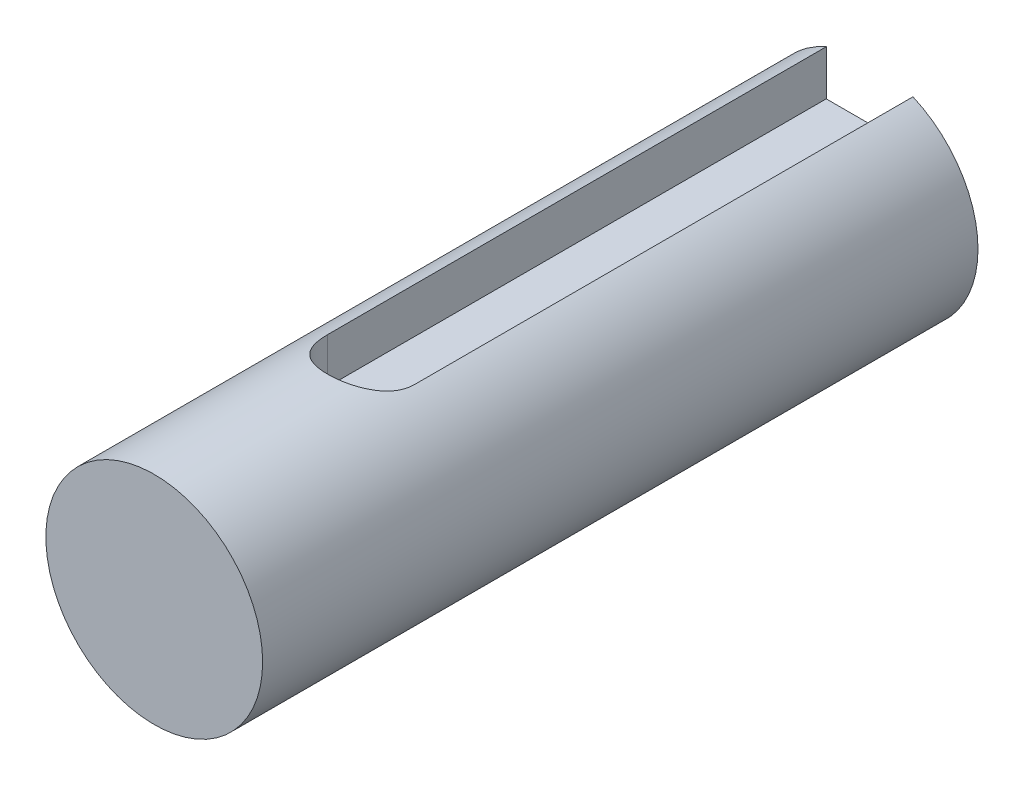
SolidWorks part; units mm, degrees
material "1023 Carbon Steel Sheet (SS)"
ref_plane "Front Plane" through (0, 0, 0) normal (0, 0, 1) x (1, 0, 0)
ref_plane "Top Plane" through (0, 0, 0) normal (0, 1, 0) x (1, 0, 0)
ref_plane "Right Plane" through (0, 0, 0) normal (1, 0, 0) x (0, 0, -1)
sketch "Sketch2" plane through (0, 0, 0) normal (0, 0, 1) x (1, 0, 0)
  line L1 (0, 0) -> (60, 0)
  line L2 (0, 0) -> (0, 60)
  line L3 (0, 60) -> (60, 60)
  line L4 (60, 0) -> (60, 60)
  dimension "D1" = 60
  dimension "D2" = 60
extrude "Boss-Extrude1" add sketch "Sketch2" along normal blind 42
sketch "Sketch3" plane through (0, 0, 0) normal (0, 0, -1) x (-1, 0, 0)
  line L4 (0, 0) -> (0, 60)
  line L5 (0, 60) -> (-60, 60)
  line L6 (-60, 60) -> (-60, 0)
  line L7 (-60, 0) -> (0, 0)
  line L8 (0, 0) -> (0, 60)
  line L9 (0, 60) -> (-60, 60)
  line L10 (-60, 60) -> (-60, 0)
  line L11 (-60, 0) -> (0, 0)
  dimension "D1" = 0
extrude "Boss-Extrude2" add sketch "Sketch3" along normal blind 38 separate body
fillet "Fillet1" radius 5 4 edges at (0, 0, 21) (60, 0, 21) (0, 60, 21) (60, 60, 21)
fillet "Fillet2" radius 5 4 edges at (0, 0, -19) (60, 0, -19) (60, 60, -19) (0, 60, -19)
fillet "Fillet3" radius 5 8 edges at (1.4645, 1.4645, 42) (0, 30, 42) (1.4645, 58.5355, 42) (30, 60, 42) (58.5355, 58.5355, 42) (60, 30, 42) (58.5355, 1.4645, 42) (30, 0, 42)
sketch "Sketch4" plane through (0, 0, -38) normal (0, 0, -1) x (-1, 0, 0)
  line L0 (-30, 60) -> (-30, 0) construction
  line L1 (-5, 60) -> (-55, 60) construction
  line L2 (-55, 0) -> (-5, 0) construction
  line L3 (-30, 30) -> (-1.4645, 58.5355) construction
  line L4 (-30, 30) -> (5, 30) construction
  circle A0 centre (-30, 30) radius 35 construction
  arc A1 (0, 55) -> (-5, 60) centre (-5, 55) ccw construction
  circle A2 centre (-5.2513, 54.7487) radius 2.25
  circle A3 centre (-54.7487, 54.7487) radius 2.25
  circle A4 centre (-54.7487, 5.2513) radius 2.25
  circle A5 centre (-5.2513, 5.2513) radius 2.25
  dimension "D1" = 70
  dimension "D2" = 4.5
extrude "Cut-Extrude1" cut sketch "Sketch4" against normal blind 10
sketch "Sketch5" plane through (0, 0, -38) normal (0, 0, -1) x (-1, 0, 0)
  line L0 (-30, 60) -> (-30, 0) construction
  line L1 (-5, 60) -> (-55, 60) construction
  line L2 (-55, 0) -> (-5, 0) construction
  line L3 (-30, 30) -> (0, 30) construction
  line L4 (0, 5) -> (0, 55) construction
  line L5 (0, 55) -> (0, 5) construction
  circle A0 centre (-30, 40) radius 12
  point P14 (-30, 28)
  point P18 (0, 30)
  dimension "D1" = 24
  dimension "D2" = 2
extrude "Boss-Extrude3" add sketch "Sketch5" along normal blind 4
sketch "Sketch6" plane through (0, 0, -42) normal (0, 0, -1) x (-1, 0, 0)
  line L0 (-30, 28) -> (-30, 40) construction
  circle A0 centre (-30, 40) radius 12 construction
  circle A1 centre (-30, 40) radius 5
  dimension "D2" = 10
  dimension "D1" = 12
extrude "Boss-Extrude4" add sketch "Sketch6" along normal blind 28 contours A1
ref_plane "Plane1" through (0, 42.5, 0) normal (0, 1, 0) x (1, 0, 0)
sketch "Sketch7" plane through (0, 42.5, 0) normal (0, 1, 0) x (1, 0, 0)
  line L0 (30, 70) -> (30, 45) construction
  line L1 (35, 70) -> (25, 70) construction
  line L2 (28, 47) -> (28, 70)
  line L3 (28, 70) -> (32, 70)
  line L4 (32, 70) -> (32, 47)
  arc A0 (28, 47) -> (32, 47) centre (30, 47) ccw
  dimension "D2" = 4
  dimension "D1" = 25
extrude "Cut-Extrude2" cut sketch "Sketch7" along normal blind 28
ref_plane "Plane2" through (30, 0, 0) normal (-1, 0, 0) x (0, 0, 1)
sketch "Sketch8" plane through (0, 0, -42) normal (0, 0, -1) x (-1, 0, 0)
  line L1 (-75.2279, -6.5935) -> (8.1794, -6.5935)
  line L2 (-75.2279, -6.5935) -> (-75.2279, 68.5905)
  line L3 (-75.2279, 68.5905) -> (8.1794, 68.5905)
  line L4 (8.1794, -6.5935) -> (8.1794, 68.5905)
extrude "Cut-Extrude3" cut sketch "Sketch8" against normal up to surface (84 mm away) contours L3 L4 L1 L2 up to face at (30, 30, 42)
sketch "Sketch9" plane through (0, 0, -42) normal (0, 0, 1) x (1, 0, 0)
  circle A0 centre (30, 40) radius 5
extrude "Boss-Extrude5" add sketch "Sketch9" along normal blind 5
